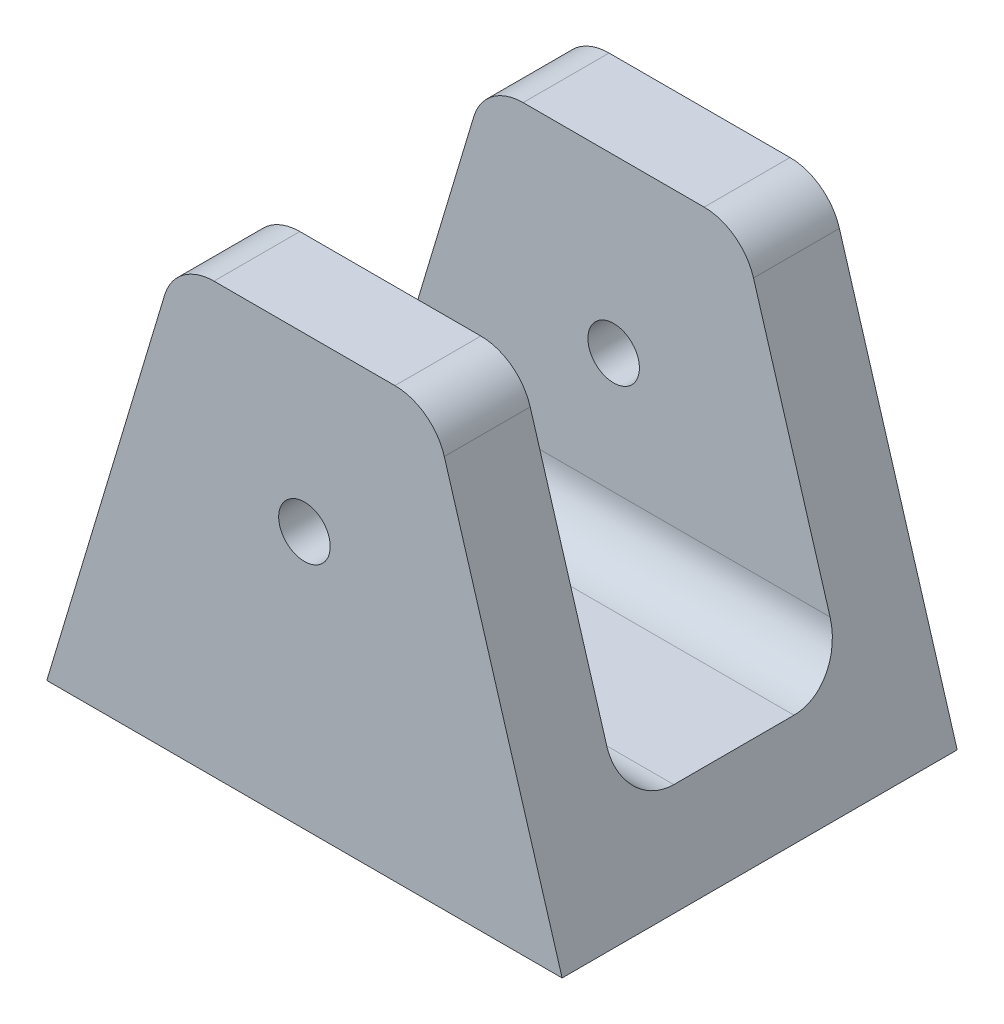
SolidWorks part; units mm, degrees
ref_plane "Ön Düzlem" through (0, 0, 0) normal (0, 0, 1) x (1, 0, 0)
ref_plane "Üst Düzlem" through (0, 0, 0) normal (0, 1, 0) x (1, 0, 0)
ref_plane "Sağ Düzlem" through (0, 0, 0) normal (1, 0, 0) x (0, 0, -1)
sketch "Sketch1" plane through (0, 0, 0) normal (0, 0, 1) x (1, 0, 0)
  line L1 (-15, 0) -> (15, 0)
  line L3 (-5.2679, 25) -> (5.2679, 25)
  line L6 (-15, 0) -> (-8.1414, 22.862)
  line L8 (8.1414, 22.862) -> (15, 0)
  circle A2 centre (0, 15) radius 1.5
  arc A3 (5.2679, 25) -> (8.1414, 22.862) centre (5.2679, 22) cw
  arc A4 (-5.2679, 25) -> (-8.1414, 22.862) centre (-5.2679, 22) ccw
  point P1 (0, 25)
  point P4 (0, 0)
  point P8 (7.5, 25)
  point P12 (-7.5, 25)
  dimension "D4" = 3
  dimension "D5" = 3
  dimension "D1" = 15
  dimension "D2" = 30
  dimension "D3" = 25
  dimension "D6" = 10
extrude "Boss-Extrude1" add sketch "Sketch1" along normal blind 23
sketch "Sketch2" plane through (0, 0, 0) normal (1, 0, 0) x (0, 0, -1)
  line L1 (-18, 5) -> (-5, 5)
  line L2 (-18, 5) -> (-18, 28.1293)
  line L3 (-18, 28.1293) -> (-5, 28.1293)
  line L4 (-5, 5) -> (-5, 28.1293)
  line L8 (-23, 0) -> (-23, 22.862) construction
  line L9 (0, 0) -> (0, 22.862) construction
  line L10 (-23, 0) -> (0, 0) construction
  dimension "D1" = 5
  dimension "D2" = 5
  dimension "D3" = 5
extrude "Cut-Extrude1" cut sketch "Sketch2" against normal through all both and the other way through all
fillet "Fillet1" radius 3 2 edges at (0, 5, 18) (0, 5, 5)
sketch "Sketch3" plane through (0, 5, 0) normal (0, 1, 0) x (1, 0, 0)
  line L0 (-13.5, -15) -> (-13.5, -8) construction
  circle A0 centre (0, -11.5) radius 1.5
  point P4 (-13.5, -11.5)
  dimension "D1" = 3
extrude "Cut-Extrude2" cut sketch "Sketch3" against normal through all
